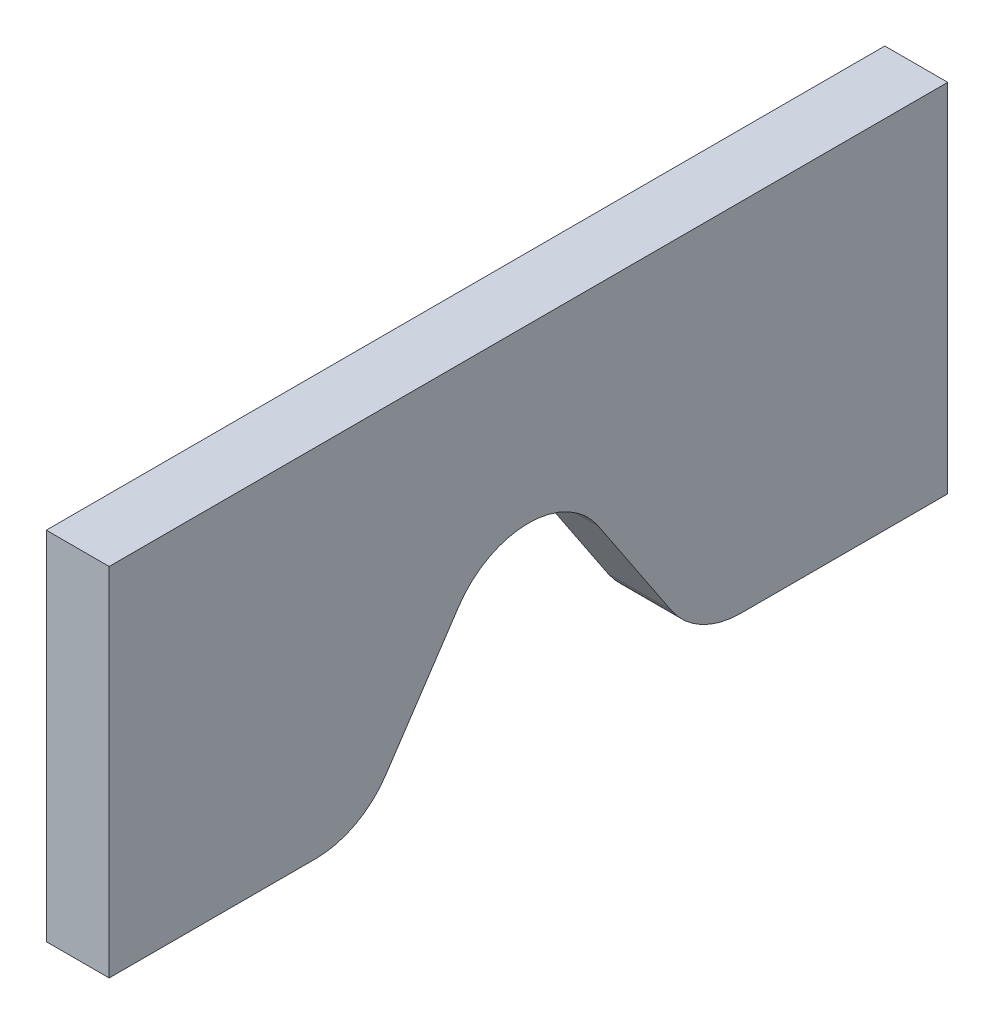
SolidWorks part; units mm, degrees
ref_plane "Front Plane" through (0, 0, 0) normal (0, 0, 1) x (1, 0, 0)
ref_plane "Top Plane" through (0, 0, 0) normal (0, 1, 0) x (1, 0, 0)
ref_plane "Right Plane" through (0, 0, 0) normal (1, 0, 0) x (0, 0, -1)
sketch "Sketch1" plane through (0, 0, 0) normal (1, 0, 0) x (0, 0, -1)
  line L0 (0, 0) -> (50000, 0) construction
  line L1 (-127, 0) -> (-127, 107.95)
  line L2 (-127, 107.95) -> (127, 107.95)
  line L3 (127, 107.95) -> (127, 0)
  line L4 (127, 0) -> (64.3937, 0)
  line L5 (43.2596, 11.3106) -> (21.1341, 44.4989)
  line L6 (-21.1341, 44.4989) -> (-43.2596, 11.3106)
  line L7 (-64.3937, 0) -> (-127, 0)
  line L8 (0, 0) -> (0, 148.1569) construction
  arc A0 (-43.2596, 11.3106) -> (-64.3937, 0) centre (-64.3937, 25.4) cw
  arc A1 (64.3937, 0) -> (43.2596, 11.3106) centre (64.3937, 25.4) cw
  arc A2 (21.1341, 44.4989) -> (-21.1341, 44.4989) centre (0, 30.4095) ccw
  point P7 (0, 0)
  point P13 (0, 107.95)
  point P14 (0, 0)
  point P15 (0, 0)
  point P18 (-50.8, 0)
  point P21 (50.8, 0)
  point P24 (0, 76.2)
  dimension "D5" = 25.4
  dimension "D1" = 107.95
  dimension "D2" = 76.2
  dimension "D3" = 76.2
  dimension "D4" = 254
extrude "Boss-Extrude1" add sketch "Sketch1" along normal blind 19.05
